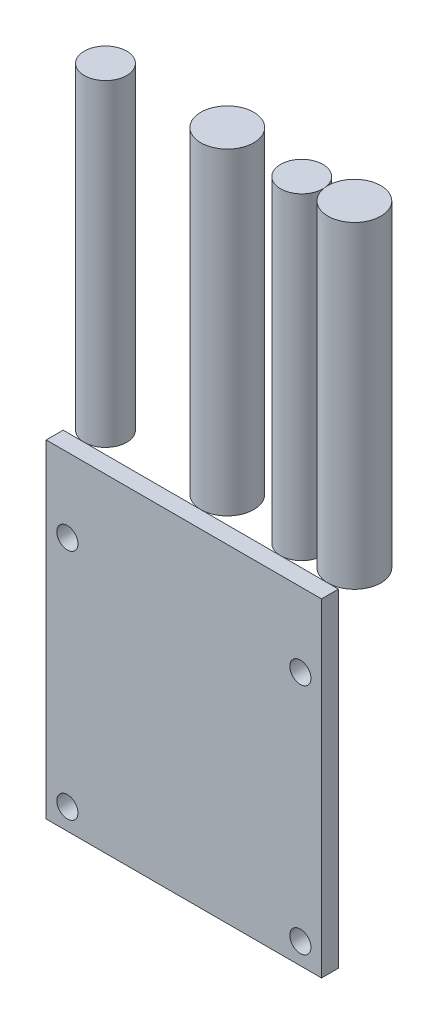
SolidWorks part; units mm, degrees
ref_plane "Front Plane" through (0, 0, 0) normal (0, 0, 1) x (1, 0, 0)
ref_plane "Top Plane" through (0, 0, 0) normal (0, 1, 0) x (1, 0, 0)
ref_plane "Right Plane" through (0, 0, 0) normal (1, 0, 0) x (0, 0, -1)
sketch "Эскиз1" plane through (0, 0, 0) normal (0, 0, 1) x (1, 0, 0)
  line L0 (0, 8.9463) -> (0, -9.8691) construction
  line L1 (-13, -15.5) -> (13, -15.5)
  line L2 (-13, -15.5) -> (-13, 15.5)
  line L3 (-13, 15.5) -> (13, 15.5)
  line L4 (13, -15.5) -> (13, 15.5)
  line L5 (-13, -15.5) -> (13, 15.5) construction
  line L6 (-13, 15.5) -> (13, -15.5) construction
  line L7 (-5.1042, 0) -> (7.2479, 0) construction
  line L8 (11, -13.5) -> (11, 7.6328) construction
  circle A0 centre (-11, -13.5) radius 1
  circle A1 centre (11, -13.5) radius 1
  circle A2 centre (11, 8.5) radius 1
  circle A3 centre (-11, 8.5) radius 1
  point P0 (0, 0)
  dimension "D3" = 2
  dimension "D6" = 22
  dimension "D1" = 26
  dimension "D2" = 31
  dimension "D4" = 2
  dimension "D5" = 2
extrude "Бобышка-Вытянуть1" add sketch "Эскиз1" along normal mid plane 1.6
sketch "Эскиз3" plane through (0, 15.5, 0) normal (0, 1, 0) x (1, 0, 0)
  line L0 (-11, 4.2932) -> (-11, -4.9861) construction
  line L1 (0, 3.8111) -> (0, -6.2515) construction
  line L2 (7.5279, 4.6648) -> (7.5279, -5.5785) construction
  line L3 (12, 3.8111) -> (12, -5.9502) construction
  line L4 (13, 0.8) -> (-13, 0.8)
  line L5 (-13, 0.8) -> (-13, -0.8)
  line L6 (-13, -0.8) -> (13, -0.8)
  line L7 (13, -0.8) -> (13, 0.8)
  line L10 (-13, -0.8) -> (-11, -0.8)
  line L12 (-13, -0.8) -> (-13, 0.8) construction
  line L13 (13, 0.8) -> (-13, 0.8) construction
  line L14 (13, -0.8) -> (13, 0.8) construction
  circle A0 centre (-11, 2.8) radius 2
  circle A1 centre (0, 3.3) radius 2.5
  circle A2 centre (12, 3.3) radius 2.5
  circle A3 centre (7.5279, 2.8) radius 2
  dimension "D2" = 2
  dimension "D3" = 4
  dimension "D4" = 5
  dimension "D6" = 4
  dimension "D5" = 1
  dimension "D1" = 0
extrude "Бобышка-Вытянуть2" add sketch "Эскиз3" along normal blind 30 separate body contours A0 | A1 | A3 | A2
